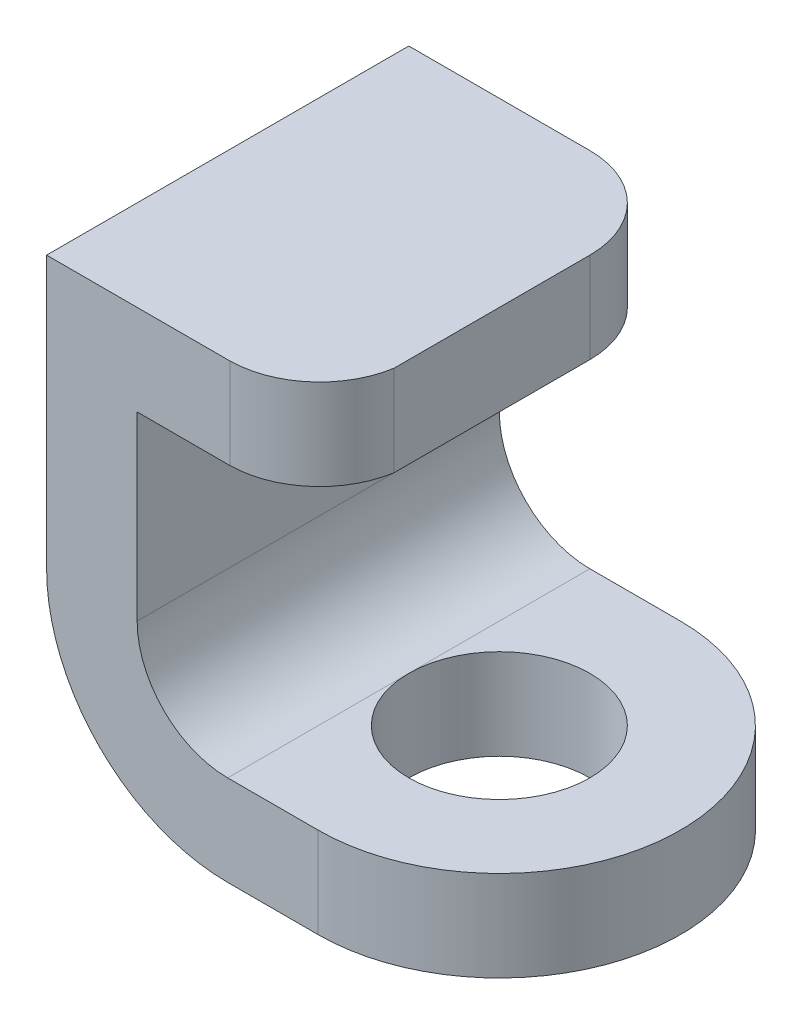
SolidWorks part; units mm, degrees
ref_plane "Front Plane" through (0, 0, 0) normal (0, 0, 1) x (1, 0, 0)
ref_plane "Top Plane" through (0, 0, 0) normal (0, 1, 0) x (1, 0, 0)
ref_plane "Right Plane" through (0, 0, 0) normal (1, 0, 0) x (0, 0, -1)
sketch "Sketch1" plane through (0, 0, 0) normal (0, 0, 1) x (1, 0, 0)
  line L0 (0, 0) -> (-30, 0)
  line L1 (-30, 0) -> (-30, -30)
  line L2 (-10, -50) -> (20, -50)
  arc A0 (-30, -30) -> (-10, -50) centre (-10, -30) ccw
  dimension "D1" = 20
  dimension "D2" = 50
  dimension "D3" = 50
  dimension "D4" = 30
extrude "Extrude-Thin1" add sketch "Sketch1" along normal blind 40 thin thin type one direction reverse wall 10
sketch "Sketch3" plane through (0, 0, 0) normal (0, 1, 0) x (1, 0, 0)
  line L0 (0, -40) -> (-30, -40) construction
  line L1 (0, -40) -> (0, 0) construction
  line L2 (0, 0) -> (-30, 0) construction
  arc A0 (-10, -40) -> (0, -31.6501) centre (-9.8631, -30.0009) ccw
  arc A1 (0, -10) -> (-10, 0) centre (-10, -10) ccw
  dimension "D1" = 10
  dimension "D6" = 10
  dimension "D2" = 10
  dimension "D3" = 8.3499
  dimension "D4" = 10
  dimension "D5" = 10
extrude "Cut-Extrude-Thin1" cut sketch "Sketch3" against normal blind 10 thin
sketch "Sketch10" plane through (0, -40, 0) normal (0, 1, 0) x (1, 0, 0)
  line L0 (-10, 0) -> (20, 0) construction
  line L1 (20, -40) -> (20, 0) construction
  line L2 (0, -40) -> (0, 0) construction
  arc A0 (0, -40) -> (0, 0) centre (0, -20) ccw
  circle A1 centre (0, -20) radius 10
  line M1 (20, 0) -> (-10, 0)
  line M3 (-10, -40) -> (20, -40)
  line M4 (20, -40) -> (20, 0)
  dimension "D1" = 20
  dimension "D2" = 40
extrude "Cut-Extrude2" cut sketch "Sketch10" against normal blind 10 contours A0 M4 M1 | A0 M3 M4 | A1 L2 | L2 A1
